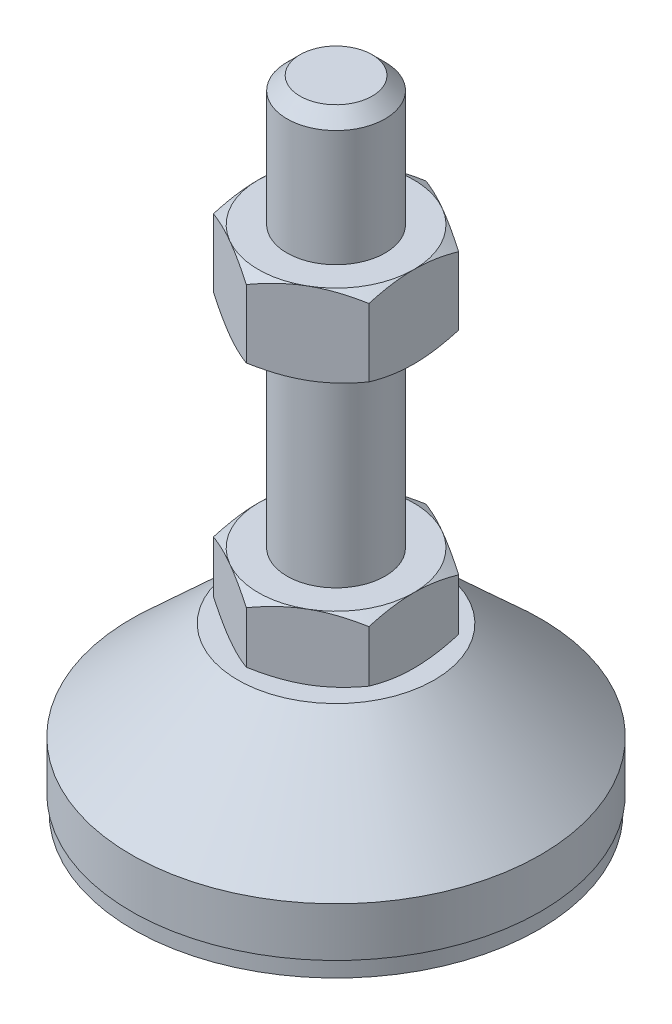
SolidWorks part; units mm, degrees
ref_plane "Спереди" through (0, 0, 0) normal (0, 0, 1) x (1, 0, 0)
ref_plane "Сверху" through (0, 0, 0) normal (0, 1, 0) x (1, 0, 0)
ref_plane "Справа" through (0, 0, 0) normal (1, 0, 0) x (0, 0, -1)
sketch "Эскиз1" plane through (0, 0, 0) normal (0, 0, 1) x (1, 0, 0)
  line L0 (0, 0) -> (-24.8, 0)
  line L1 (-24.8, 0) -> (-24.8, 2)
  line L2 (-24.8, 2) -> (-25, 2)
  line L3 (-25, 2) -> (-25, 8)
  line L4 (-25, 8) -> (-12, 20)
  line L5 (-12, 20) -> (-6, 20)
  line L12 (-6, 28) -> (-6, 76.4)
  line L13 (-6, 76.4) -> (-4.4, 78)
  line L14 (-4.4, 78) -> (0, 78)
  line L15 (0, 78) -> (0, 0) construction
  line L16 (-6, 20) -> (0, 20) construction
  line L17 (0, 0) -> (0, 78)
  line L18 (0, 0) -> (0, -7.9595) construction
  line L19 (-6, 28) -> (-6, 20)
  point P8 (-6, 52.2)
  point P23 (-9, 20)
  dimension "D1" = 12
  dimension "D2" = 20
  dimension "D3" = 8
  dimension "D4" = 50
  dimension "D5" = 6
  dimension "D6" = 1.6
  dimension "D7" = 45
  dimension "D8" = 24
  dimension "D9" = 2
  dimension "D10" = 50
  dimension "D11" = 6
  dimension "D12" = 0.2
revolve "Повернуть1" add sketch "Эскиз1" angle 360 about L17
sketch "Эскиз2" plane through (0, 20, 0) normal (0, 1, 0) x (1, 0, 0)
  line L1 (0, 10.9697) -> (-9.5, 5.4848)
  line L2 (-9.5, 5.4848) -> (-9.5, -5.4848)
  line L3 (-9.5, -5.4848) -> (0, -10.9697)
  line L4 (0, -10.9697) -> (9.5, -5.4848)
  line L5 (9.5, -5.4848) -> (9.5, 5.4848)
  line L6 (9.5, 5.4848) -> (0, 10.9697)
  circle A0 centre (0, 0) radius 9.5 construction
  dimension "D1" = 19
extrude "Бобышка-Вытянуть1" add sketch "Эскиз2" along normal up to vertex (8 mm away) up to point (-6, 28, 0)
ref_plane "Плоскость1" through (0, 52.2, 0) normal (0, 1, 0) x (1, 0, 0)
sketch "Эскиз3" plane through (0, 52.2, 0) normal (0, 1, 0) x (1, 0, 0)
  line L6 (9.5, 5.4848) -> (0, 10.9697)
  line L7 (0, 10.9697) -> (-9.5, 5.4848)
  line L8 (-9.5, 5.4848) -> (-9.5, -5.4848)
  line L9 (-9.5, -5.4848) -> (0, -10.9697)
  line L10 (0, -10.9697) -> (9.5, -5.4848)
  line L11 (9.5, -5.4848) -> (9.5, 5.4848)
  line L12 (9.5, 5.4848) -> (0, 10.9697)
  line L13 (0, 10.9697) -> (-9.5, 5.4848)
  line L14 (-9.5, 5.4848) -> (-9.5, -5.4848)
  line L15 (-9.5, -5.4848) -> (0, -10.9697)
  line L16 (0, -10.9697) -> (9.5, -5.4848)
  line L17 (9.5, -5.4848) -> (9.5, 5.4848)
  dimension "D1" = 0
extrude "Бобышка-Вытянуть2" add sketch "Эскиз3" along normal blind 10
sketch "Эскиз4" plane through (0, 0, 0) normal (0, 0, 1) x (1, 0, 0)
  line L0 (-9.5, 62.2) -> (-18.1603, 57.2)
  line L1 (-18.1603, 57.2) -> (-18.1603, 62.2)
  line L2 (-18.1603, 62.2) -> (-9.5, 62.2)
  line L3 (-18.1603, 57.2) -> (-9.5, 52.2)
  line L4 (50, 52.2) -> (-50, 52.2) construction
  line L5 (-9.5, 52.2) -> (-18.1603, 52.2)
  line L6 (-18.1603, 52.2) -> (-18.1603, 57.2)
  line L7 (-9.5, 62.2) -> (-9.5, 52.2) construction
  line L8 (-9.5, 28) -> (-16.4282, 28)
  line L9 (-16.4282, 28) -> (-16.4282, 24)
  line L10 (-16.4282, 24) -> (-9.5, 28)
  line L11 (-9.5, 20) -> (-16.4282, 24)
  line L12 (-16.4282, 24) -> (-16.4282, 20)
  line L13 (-16.4282, 20) -> (-9.5, 20)
  line L14 (0, 78) -> (0, 96.3793) construction
  dimension "D1" = 30
  dimension "D2" = 30
revolve "Вырез-Повернуть2" cut sketch "Эскиз4" angle 360 about L14
